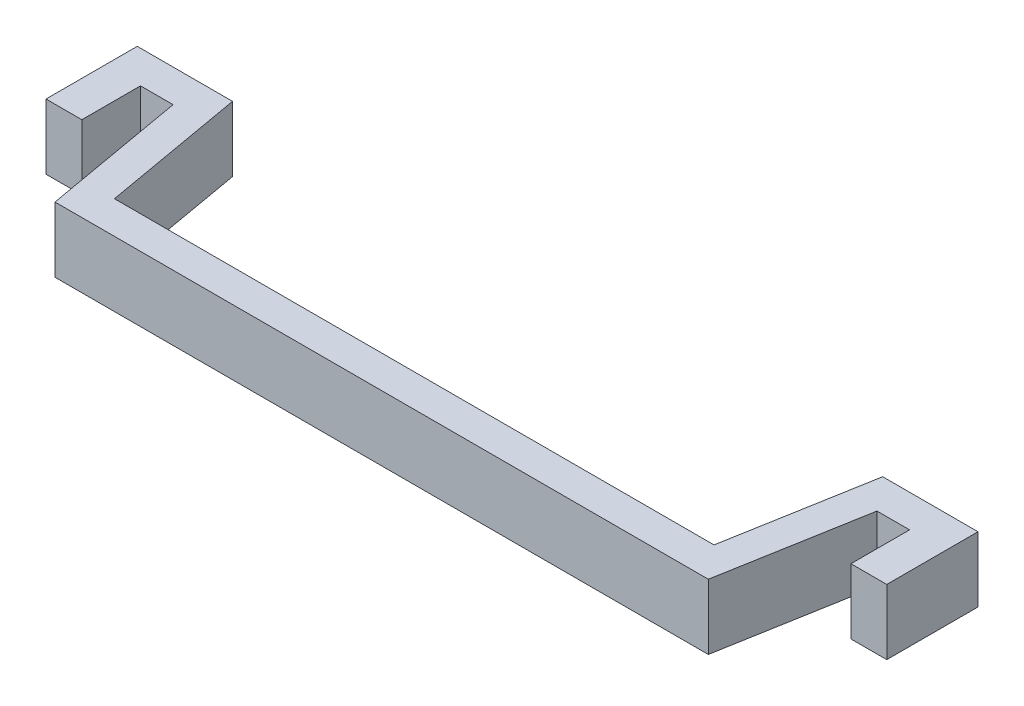
SolidWorks part; units mm, degrees
ref_plane "Front Plane" through (0, 0, 0) normal (0, 0, 1) x (1, 0, 0)
ref_plane "Top Plane" through (0, 0, 0) normal (0, 1, 0) x (1, 0, 0)
ref_plane "Right Plane" through (0, 0, 0) normal (1, 0, 0) x (0, 0, -1)
sketch "Sketch1" plane through (0, 0, 0) normal (0, 1, 0) x (1, 0, 0)
  line L0 (0, 0) -> (0, 6.858) construction
  line L1 (12.7307, 0) -> (-12.7307, 0)
  line L2 (-12.7307, 0) -> (-13.716, 5.588)
  line L3 (-13.716, 5.588) -> (-14.986, 5.588)
  line L4 (-14.986, 5.588) -> (-14.986, 3.302)
  line L5 (-14.986, 3.302) -> (-16.383, 3.302)
  line L6 (-16.383, 3.302) -> (-16.383, 6.858)
  line L7 (-16.383, 6.858) -> (-12.6693, 6.858)
  line L8 (-12.6693, 6.858) -> (-11.684, 1.27)
  line L9 (-11.684, 1.27) -> (11.684, 1.27)
  line L10 (12.6693, 6.858) -> (11.684, 1.27)
  line L11 (16.383, 6.858) -> (12.6693, 6.858)
  line L12 (16.383, 3.302) -> (16.383, 6.858)
  line L13 (14.986, 3.302) -> (16.383, 3.302)
  line L14 (14.986, 5.588) -> (14.986, 3.302)
  line L15 (13.716, 5.588) -> (14.986, 5.588)
  line L16 (12.7307, 0) -> (13.716, 5.588)
  point P13 (0, 1.27)
  dimension "D1" = 1.27
  dimension "D2" = 1.397
  dimension "D3" = 4.318
  dimension "D4" = 13.716
  dimension "D5" = 11.684
  dimension "D6" = 2.286
  dimension "D7" = 1.27
  dimension "D8" = 1.27
  dimension "D9" = 100
extrude "Boss-Extrude1" add sketch "Sketch1" along normal blind 2.54
